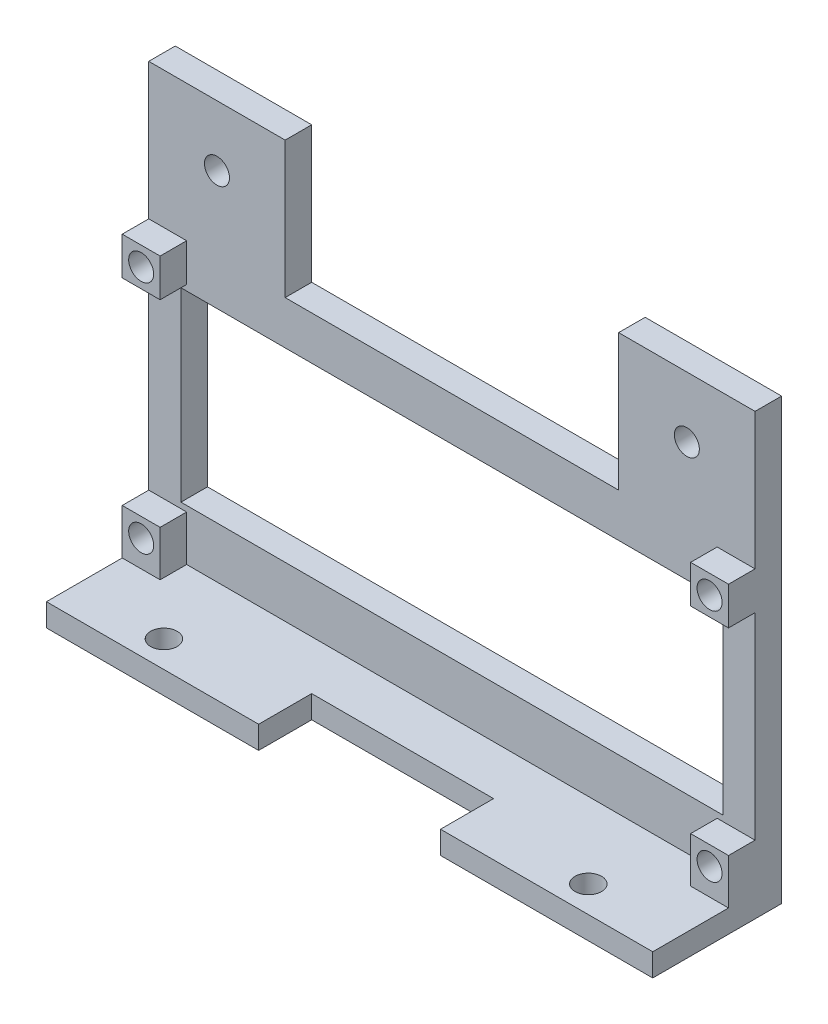
SolidWorks part; units mm, degrees
ref_plane "Front Plane" through (0, 0, 0) normal (0, 0, 1) x (1, 0, 0)
ref_plane "Top Plane" through (0, 0, 0) normal (0, 1, 0) x (1, 0, 0)
ref_plane "Right Plane" through (0, 0, 0) normal (1, 0, 0) x (0, 0, -1)
sketch "Sketch1" plane through (0, 0, 0) normal (0, 0, 1) x (1, 0, 0)
  line L0 (-1.75, 27.75) -> (-1.75, 30.25) construction
  line L1 (0, 0) -> (71.5, 0)
  line L2 (0, 0) -> (0, 24.5)
  line L3 (0, 24.5) -> (71.5, 24.5)
  line L4 (71.5, 0) -> (71.5, 24.5)
  line L5 (-4.25, -5.75) -> (75.75, -5.75)
  line L6 (-4.25, -5.75) -> (-4.25, 30.25)
  line L7 (-4.25, 30.25) -> (75.75, 30.25)
  line L8 (75.75, -5.75) -> (75.75, 30.25)
  line L9 (-1.75, 27.75) -> (-4.25, 27.75) construction
  circle A4 centre (-1.75, 27.75) radius 1.65
  circle A5 centre (73.25, 27.75) radius 1.65
  circle A6 centre (73.25, -3.25) radius 1.65
  circle A7 centre (-1.75, -3.25) radius 1.65
  point P9 (-4.25, 12.25)
  point P10 (0, 12.25)
  point P11 (35.75, 0)
  point P12 (35.75, -5.75)
  dimension "D3" = 2.5
  dimension "D4" = 2.5
  dimension "D7" = 3.3
  dimension "D8" = 2.5
  dimension "D9" = 2.5
  dimension "D10" = 2.5
  dimension "D11" = 2.5
  dimension "D12" = 2.5
  dimension "D13" = 2.5
  dimension "D1" = 24.5
  dimension "D2" = 71.5
  dimension "D5" = 36
  dimension "D6" = 80
extrude "Boss-Extrude1" add sketch "Sketch1" along normal blind 3.5
sketch "Sketch2" plane through (0, 0, 3.5) normal (0, 0, 1) x (1, 0, 0)
  line L1 (-4.25, 30.25) -> (0.75, 30.25)
  line L2 (-4.25, 30.25) -> (-4.25, 25.25)
  line L3 (-4.25, 25.25) -> (0.75, 25.25)
  line L4 (0.75, 30.25) -> (0.75, 25.25)
  line L5 (75.75, 30.25) -> (70.75, 30.25)
  line L6 (75.75, 30.25) -> (75.75, 25.25)
  line L7 (75.75, 25.25) -> (70.75, 25.25)
  line L8 (70.75, 30.25) -> (70.75, 25.25)
  line L9 (-4.25, -5.75) -> (0.75, -5.75)
  line L10 (-4.25, -5.75) -> (-4.25, -0.75)
  line L11 (-4.25, -0.75) -> (0.75, -0.75)
  line L12 (0.75, -5.75) -> (0.75, -0.75)
  line L13 (75.75, -5.75) -> (70.75, -5.75)
  line L14 (75.75, -5.75) -> (75.75, -0.75)
  line L15 (75.75, -0.75) -> (70.75, -0.75)
  line L16 (70.75, -5.75) -> (70.75, -0.75)
  circle A0 centre (-1.75, 27.75) radius 1.65
  circle A1 centre (73.25, 27.75) radius 1.65
  circle A2 centre (73.25, -3.25) radius 1.65
  circle A3 centre (-1.75, -3.25) radius 1.65
  dimension "D1" = 2.5
  dimension "D2" = 2.5
  dimension "D3" = 2.5
  dimension "D4" = 2.5
  dimension "D5" = 3.3
extrude "Boss-Extrude2" add sketch "Sketch2" along normal blind 3.5
sketch "Sketch3" plane through (0, -5.75, 0) normal (0, -1, 0) x (-1, 0, 0)
  line L0 (-47.75, -17) -> (-47.75, -10)
  line L1 (4.25, 0) -> (-75.75, 0)
  line L2 (4.25, 0) -> (4.25, -17)
  line L3 (4.25, -17) -> (-23.75, -17)
  line L4 (-75.75, 0) -> (-75.75, -17)
  line L5 (-47.75, -10) -> (-23.75, -10)
  line L6 (-23.75, -10) -> (-23.75, -17)
  line L7 (-47.75, -17) -> (-75.75, -17)
  circle A0 centre (-7.75, -13.5) radius 1.75
  circle A1 centre (-63.75, -13.5) radius 1.75
  dimension "D2" = 3.5
  dimension "D3" = 3.5
  dimension "D4" = 12
  dimension "D5" = 3.5
  dimension "D6" = 12
  dimension "D1" = 17
  dimension "D7" = 28
  dimension "D8" = 28
  dimension "D9" = 7
sketch "Sketch6" plane through (0, -5.75, 0) normal (0, -1, 0) x (1, 0, 0)
  line L0 (-4.25, 0) -> (-4.25, 7)
  line L1 (-4.25, 7) -> (0.75, 7)
  line L2 (0.75, 7) -> (0.75, 3.5)
  line L3 (0.75, 3.5) -> (70.75, 3.5)
  line L4 (70.75, 3.5) -> (70.75, 7)
  line L5 (70.75, 7) -> (75.75, 7)
  line L6 (75.75, 7) -> (75.75, 0)
  line L7 (75.75, 0) -> (-4.25, 0)
extrude "Boss-Extrude4" add sketch "Sketch6" along normal blind 1
extrude "Boss-Extrude5" add sketch "Sketch3" along normal blind 3 from offset 1
sketch "Sketch7" plane through (0, 0, 0) normal (0, 0, -1) x (-1, 0, 0)
  line L0 (-75.75, 30.25) -> (4.25, 30.25) construction
  line L1 (-75.75, 30.25) -> (-57.75, 30.25)
  line L2 (-75.75, 30.25) -> (-75.75, 48.25)
  line L3 (-75.75, 48.25) -> (-57.75, 48.25)
  line L4 (-57.75, 30.25) -> (-57.75, 48.25)
  line L5 (4.25, 30.25) -> (-13.75, 30.25)
  line L6 (4.25, 30.25) -> (4.25, 48.25)
  line L7 (4.25, 48.25) -> (-13.75, 48.25)
  line L8 (-13.75, 30.25) -> (-13.75, 48.25)
  line L9 (-66.75, 40.25) -> (-4.75, 40.25) construction
  circle A0 centre (-66.75, 40.25) radius 1.65
  circle A1 centre (-4.75, 40.25) radius 1.65
  point P16 (-35.75, 30.25)
  dimension "D3" = 3.3
  dimension "D4" = 62
  dimension "D5" = 31
  dimension "D6" = 10
  dimension "D1" = 18
  dimension "D2" = 18
extrude "Boss-Extrude6" add sketch "Sketch7" against normal blind 3.5
